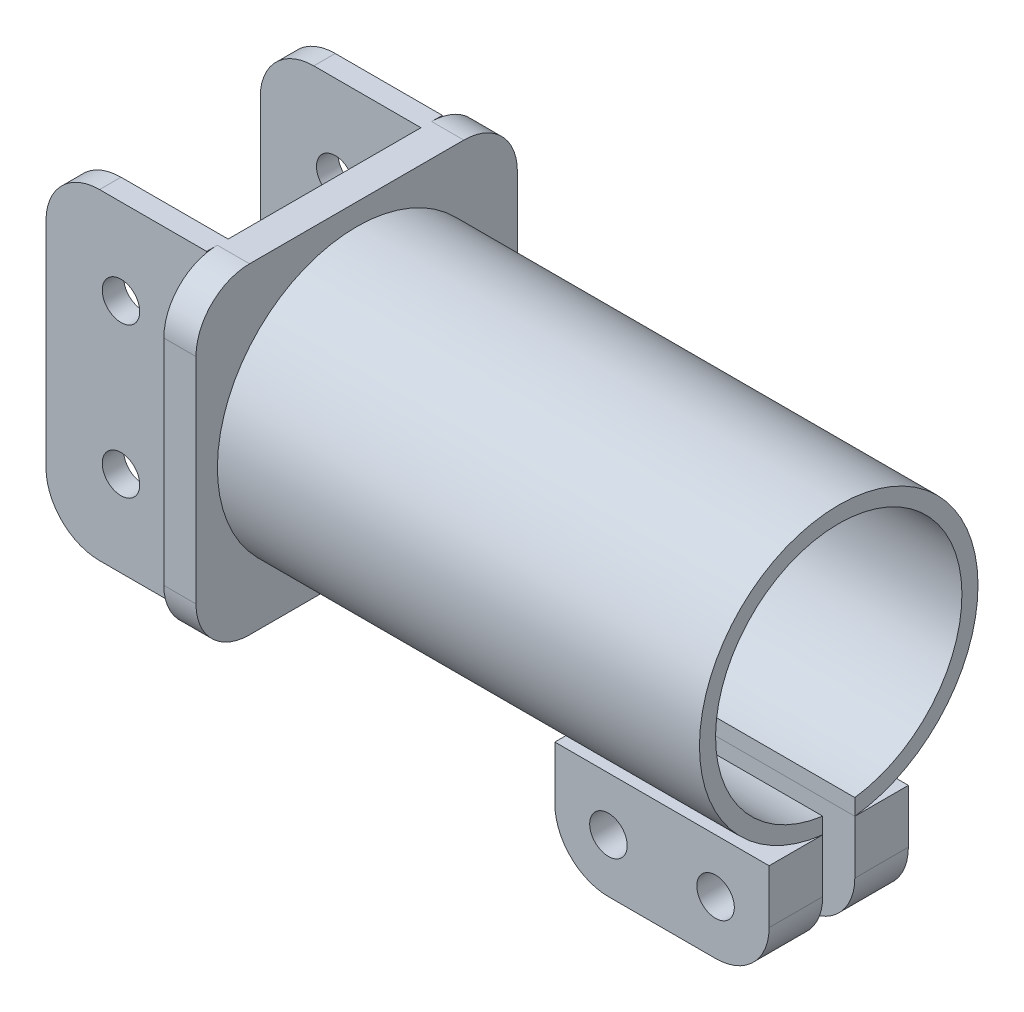
SolidWorks part; units mm, degrees
ref_plane "Front Plane" through (0, 0, 0) normal (0, 0, 1) x (1, 0, 0)
ref_plane "Top Plane" through (0, 0, 0) normal (0, 1, 0) x (1, 0, 0)
ref_plane "Right Plane" through (0, 0, 0) normal (1, 0, 0) x (0, 0, -1)
sketch "Sketch1" plane through (0, 0, 0) normal (1, 0, 0) x (0, 0, -1)
  circle A0 centre (0, 0) radius 13
  circle A1 centre (0, 0) radius 11.5
  dimension "D1" = 26
  dimension "D2" = 23
extrude "Boss-Extrude5" add sketch "Sketch1" along normal blind 45
sketch "Sketch5" plane through (0, 0, 0) normal (-1, 0, 0) x (0, 0, 1)
  line L1 (-10, 15) -> (10, 15)
  line L2 (-15, 10) -> (-15, -10)
  line L3 (-10, -15) -> (10, -15)
  line L4 (15, 10) -> (15, -10)
  line L5 (-15, 15) -> (15, -15) construction
  line L6 (-15, -15) -> (15, 15) construction
  arc A0 (-15, -10) -> (-10, -15) centre (-10, -10) ccw
  arc A1 (10, -15) -> (15, -10) centre (10, -10) ccw
  arc A2 (10, 15) -> (15, 10) centre (10, 10) cw
  arc A3 (-10, 15) -> (-15, 10) centre (-10, 10) ccw
  point P0 (0, 0)
  dimension "D3" = 5
  dimension "D1" = 30
  dimension "D2" = 30
extrude "Boss-Extrude7" add sketch "Sketch5" along normal blind 3
sketch "Sketch6" plane through (-3, 0, 0) normal (-1, 0, 0) x (0, 0, 1)
  line L0 (10, 15) -> (-10, 15) construction
  line L1 (-11, 15) -> (-9, 15)
  line L2 (-11, 15) -> (-11, -15)
  line L3 (-11, -15) -> (-9, -15)
  line L4 (-9, 15) -> (-9, -15)
  line L5 (-10, -15) -> (10, -15) construction
  line L6 (0, -16.5) -> (0, 16.5) construction
  line L7 (9, 15) -> (11, 15)
  line L8 (9, 15) -> (9, -15)
  line L9 (9, -15) -> (11, -15)
  line L10 (11, 15) -> (11, -15)
  dimension "D1" = 9
  dimension "D2" = 9
  dimension "D3" = 2
  dimension "D4" = 2
  dimension "D5" = 22
extrude "Boss-Extrude8" add sketch "Sketch6" along normal blind 15
sketch "Sketch7" plane through (0, 0, 0) normal (0, 0, 1) x (1, 0, 0)
  line L0 (45, -13) -> (45, 13) construction
  line L1 (5, -8.2307) -> (45, -8.2307)
  line L2 (5, -8.2307) -> (5, -17.9746)
  line L3 (5, -17.9746) -> (45, -17.9746)
  line L4 (45, -8.2307) -> (45, -17.9746)
  dimension "D1" = 40
extrude "Cut-Extrude1" cut sketch "Sketch7" against normal mid plane 3
fillet "Fillet1" radius 5 4 edges at (-18, -15, 10) (-18, -15, -10) (-18, 15, 10) (-18, 15, -10)
sketch "Sketch8" plane through (0, 0, 11) normal (0, 0, 1) x (1, 0, 0)
  line L0 (16.5, 0) -> (-16.5, 0) construction
  line L2 (-18, -10) -> (-18, 10) construction
  circle A0 centre (-11, 7) radius 1.75
  circle A1 centre (-11, -7) radius 1.75
  dimension "D1" = 3.5
  dimension "D2" = 7
  dimension "D3" = 7
  dimension "D4" = 7
extrude "Cut-Extrude2" cut sketch "Sketch8" against normal blind 77
sketch "Sketch9" plane through (0, 0, -1.5) normal (0, 0, 1) x (1, 0, 0)
  line L1 (45, -12.9132) -> (25, -12.9132)
  line L2 (45, -12.9132) -> (45, -17.9132)
  line L3 (40, -22.9132) -> (30, -22.9132)
  line L4 (25, -12.9132) -> (25, -17.9132)
  arc A0 (45, -17.9132) -> (40, -22.9132) centre (40, -17.9132) cw
  arc A1 (30, -22.9132) -> (25, -17.9132) centre (30, -17.9132) cw
  circle A3 centre (40, -17.9132) radius 1.75
  circle A4 centre (30, -17.9132) radius 1.75
  point P7 (45, -22.9132)
  dimension "D3" = 5
  dimension "D4" = 3.5
  dimension "D1" = 10
  dimension "D2" = 20
extrude "Boss-Extrude9" add sketch "Sketch9" against normal blind 5 separate body
sketch "Sketch12" plane through (0, 0, 1.5) normal (0, 0, -1) x (-1, 0, 0)
  line L4 (-45, -12.9132) -> (-45, -17.9132)
  line L5 (-40, -22.9132) -> (-30, -22.9132)
  line L6 (-25, -17.9132) -> (-25, -12.9132)
  line L7 (-25, -12.9132) -> (-45, -12.9132)
  line L8 (-45, -12.9132) -> (-45, -17.9132)
  line L9 (-40, -22.9132) -> (-30, -22.9132)
  line L10 (-25, -17.9132) -> (-25, -12.9132)
  line L11 (-25, -12.9132) -> (-45, -12.9132)
  circle A0 centre (-30, -17.9132) radius 1.75 construction
  circle A1 centre (-30, -17.9132) radius 1.75
  arc A2 (-45, -17.9132) -> (-40, -22.9132) centre (-40, -17.9132) ccw
  arc A3 (-30, -22.9132) -> (-25, -17.9132) centre (-30, -17.9132) ccw
  arc A4 (-45, -17.9132) -> (-40, -22.9132) centre (-40, -17.9132) ccw
  arc A5 (-30, -22.9132) -> (-25, -17.9132) centre (-30, -17.9132) ccw
  circle A6 centre (-40, -17.9132) radius 1.75 construction
  circle A7 centre (-40, -17.9132) radius 1.75
  dimension "D1" = 0
extrude "Boss-Extrude10" add sketch "Sketch12" against normal blind 5 separate body
